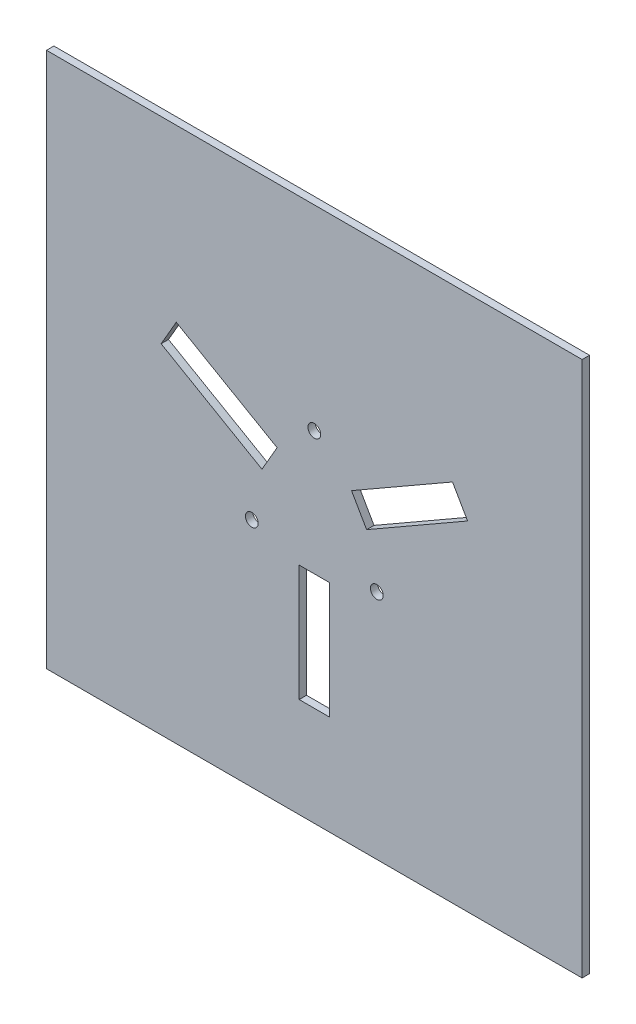
SolidWorks part; units mm, degrees
ref_plane "Front Plane" through (0, 0, 0) normal (0, 0, 1) x (1, 0, 0)
ref_plane "Top Plane" through (0, 0, 0) normal (0, 1, 0) x (1, 0, 0)
ref_plane "Right Plane" through (0, 0, 0) normal (1, 0, 0) x (0, 0, -1)
ref_plane "Plane1" through (0, 0, 3.175) normal (0, 0, 1) x (1, 0, 0)
sketch "Sketch1" plane through (0, 0, 3.175) normal (0, 0, 1) x (1, 0, 0)
  line L0 (-6.5, -22.2) -> (6.5, -22.2)
  line L1 (6.5, -22.2) -> (6.5, -72.1995)
  line L2 (6.5, -72.1995) -> (-6.5, -72.1995)
  line L3 (-6.5, -72.1995) -> (-6.5, -22.2)
  line L4 (15.989, 16.7368) -> (59.3483, 41.6349)
  line L5 (59.3483, 41.6349) -> (65.8219, 30.3614)
  line L6 (65.8219, 30.3614) -> (22.4626, 5.4632)
  line L7 (22.4626, 5.4632) -> (15.989, 16.7368)
  line L8 (-65.7766, 30.4706) -> (-59.2766, 41.7289)
  line L9 (-59.2766, 41.7289) -> (-15.9758, 16.7292)
  line L10 (-15.9758, 16.7292) -> (-22.4758, 5.4708)
  line L11 (-22.4758, 5.4708) -> (-65.7766, 30.4706)
  line L12 (-115, 115) -> (-115, -115)
  line L13 (115, -115) -> (115, 115)
  line L14 (0, 0) -> (-26.8474, -15.5004) construction
  line L15 (-19.2258, 11.1) -> (-19.2258, -11.1) construction
  line L16 (115, 115) -> (-115, 115)
  line L17 (-19.2258, -11.1) -> (0, -22.2) construction
  line L18 (0, -22.2) -> (19.2258, -11.1) construction
  line L19 (19.2258, -11.1) -> (19.2258, 11.1) construction
  line L20 (19.2258, 11.1) -> (0, 22.2) construction
  line L21 (0, 22.2) -> (-19.2258, 11.1) construction
  line L22 (-115, -115) -> (115, -115)
  line L23 (0, 31.0007) -> (0, 0) construction
  line L24 (0, 0) -> (26.8474, -15.5004) construction
  line L25 (-115, 0) -> (115, 0) construction
  line L26 (0, -115) -> (0, 115) construction
  circle A0 centre (-26.8474, -15.5004) radius 2.75
  circle A1 centre (26.8474, -15.5004) radius 2.75
  circle A2 centre (0, 31.0007) radius 2.75
  circle A3 centre (0, 0) radius 19.2258 construction
  point P32 (0, 0)
  dimension "D1" = 13
  dimension "D2" = 49.9995
  dimension "D3" = 230
  dimension "D4" = 230
extrude "Boss-Extrude1" add sketch "Sketch1" against normal blind 3.175
